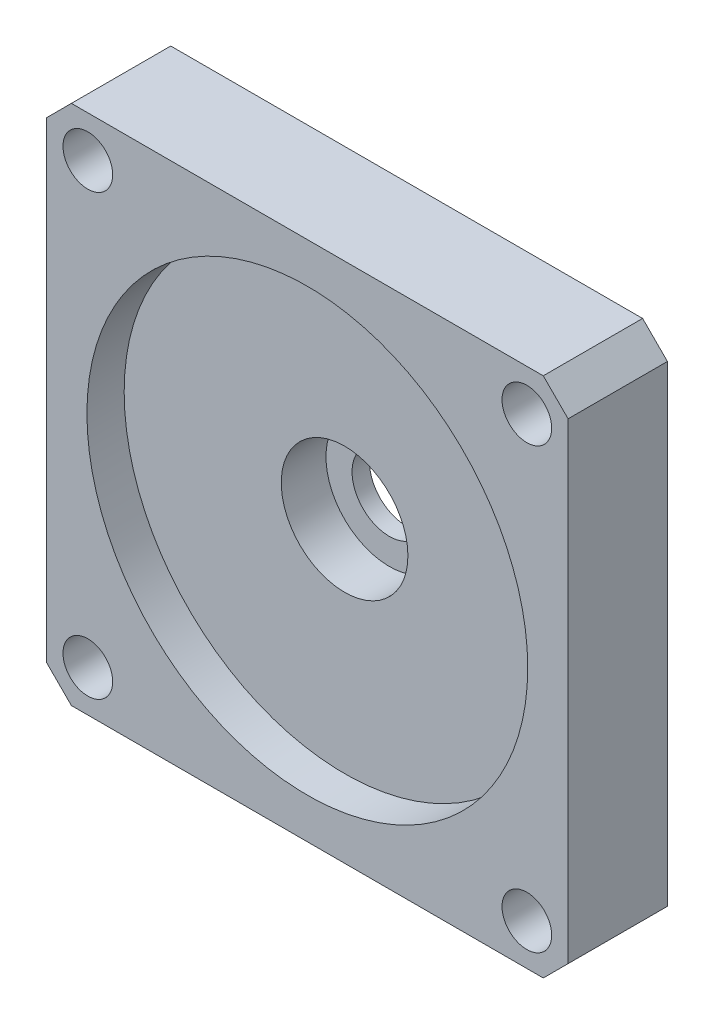
SolidWorks part; units mm, degrees
ref_plane "前视基准面" through (0, 0, 0) normal (0, 0, 1) x (1, 0, 0)
ref_plane "上视基准面" through (0, 0, 0) normal (0, 1, 0) x (1, 0, 0)
ref_plane "右视基准面" through (0, 0, 0) normal (1, 0, 0) x (0, 0, -1)
sketch "草图1" plane through (0, 0, 0) normal (0, 0, 1) x (1, 0, 0)
  line L1 (-21, 21) -> (21, 21)
  line L2 (-21, 21) -> (-21, -21)
  line L3 (-21, -21) -> (21, -21)
  line L4 (21, 21) -> (21, -21)
  line L5 (0, -21) -> (0, 21) construction
  line L6 (-21, 0) -> (21, 0) construction
  point P0 (0, 0)
  dimension "D1" = 42
  dimension "D2" = 42
extrude "凸台-拉伸1" add sketch "草图1" along normal blind 8
sketch "草图2" plane through (0, 0, 8) normal (0, 0, 1) x (1, 0, 0)
  circle A0 centre (-17.6777, 17.6777) radius 2
  circle A1 centre (17.6777, 17.6777) radius 2
  circle A2 centre (17.6777, -17.6777) radius 2
  circle A3 centre (-17.6777, -17.6777) radius 2
  point P11 (0, 0)
  dimension "D2" = 4
  dimension "D3" = 50
  dimension "D1" = 4
extrude "切除-拉伸1" cut sketch "草图2" against normal up to next
sketch "草图3" plane through (0, 0, 8) normal (0, 0, 1) x (1, 0, 0)
  circle A0 centre (0, 0) radius 17.75
  dimension "D1" = 35.5
extrude "切除-拉伸2" cut sketch "草图3" against normal blind 3
sketch "草图4" plane through (0, 0, 5) normal (0, 0, 1) x (1, 0, 0)
  circle A0 centre (0, 0) radius 5.1
  dimension "D1" = 10.2
extrude "切除-拉伸3" cut sketch "草图4" against normal blind 3.6
sketch "草图5" plane through (0, 0, 1.4) normal (0, 0, 1) x (1, 0, 0)
  circle A0 centre (0, 0) radius 3
  dimension "D1" = 6
extrude "切除-拉伸4" cut sketch "草图5" against normal up to next
chamfer "倒角1" distance 2 angle 45 4 edges at (21, -21, 4) (-21, -21, 4) (-21, 21, 4) (21, 21, 4)
